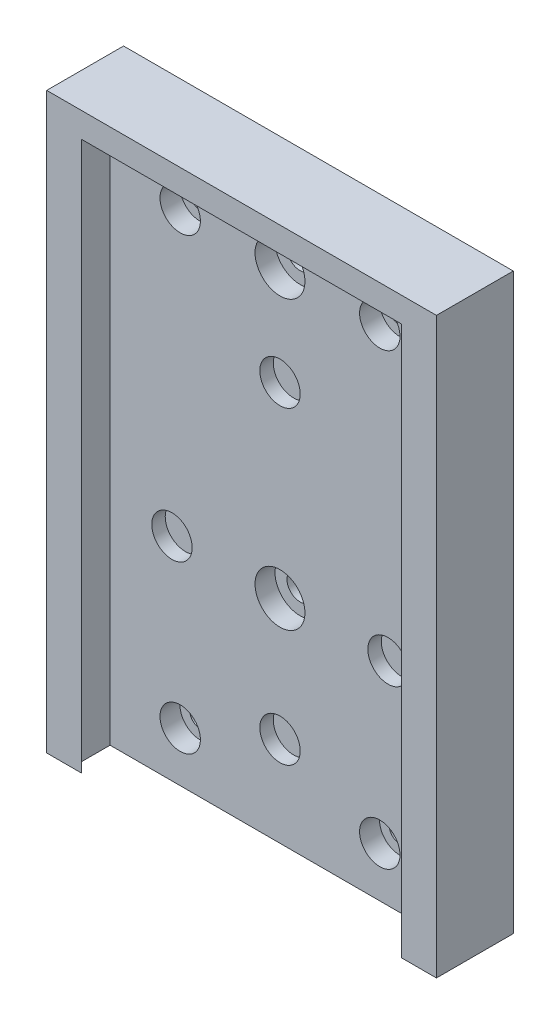
SolidWorks part; units mm, degrees
ref_plane "Front Plane" through (0, 0, 0) normal (0, 0, 1) x (1, 0, 0)
ref_plane "Top Plane" through (0, 0, 0) normal (0, 1, 0) x (1, 0, 0)
ref_plane "Right Plane" through (0, 0, 0) normal (1, 0, 0) x (0, 0, -1)
sketch "Sketch1" plane through (0, 0, 0) normal (0, 0, 1) x (1, 0, 0)
  line L0 (0, -45) -> (0, -41) construction
  line L5 (-34, 55) -> (34, -55) construction
  line L6 (-34, -55) -> (34, 55) construction
  line L7 (-20, 45) -> (20, 45) construction
  line L8 (-20, 45) -> (-20, -45) construction
  line L9 (-20, -45) -> (20, -45) construction
  line L10 (20, 45) -> (20, -45) construction
  line L11 (-20, 45) -> (20, -45) construction
  line L12 (-20, -45) -> (20, 45) construction
  line L13 (0, 25) -> (-21.6506, -12.5) construction
  line L14 (-21.6506, -12.5) -> (21.6506, -12.5) construction
  line L15 (21.6506, -12.5) -> (0, 25) construction
  line L16 (0, 45) -> (0, 55) construction
  line L17 (34.05, 55) -> (-34.05, 55)
  line L18 (0, 0) -> (-10.595, 0) construction
  line L19 (34.05, -55) -> (-34.05, -55)
  line L20 (34.05, -55) -> (34.05, 55)
  line L21 (-34.05, -55) -> (-34.05, 55)
  circle A0 centre (20, 45) radius 2.1
  circle A1 centre (-20, 45) radius 2.1
  circle A2 centre (20, -45) radius 2.1
  circle A3 centre (-20, -45) radius 2.1
  circle A4 centre (0, 0) radius 25 construction
  circle A5 centre (21.6506, -12.5) radius 4.05
  circle A6 centre (0, 25) radius 4.05
  circle A7 centre (-21.6506, -12.5) radius 4.05
  circle A9 centre (0, -36.95) radius 4.05
  circle A10 centre (0, 45) radius 2.6
  circle A11 centre (0, -12.5) radius 2.6
  point P0 (0, 0)
  point P6 (0, 0)
  point P35 (0, 55)
extrude "Boss-Extrude1" add sketch "Sketch1" along normal blind 7.7
sketch "Sketch2" plane through (0, 0, 0) normal (0, 0, -1) x (-1, 0, 0)
  circle A0 centre (-21.6506, -12.5) radius 6.3046
  circle A1 centre (0, 25) radius 7.3343
  circle A2 centre (21.6506, -12.5) radius 8.114
  circle A3 centre (0, -36.95) radius 11.0737
extrude "Boss-Extrude2" add sketch "Sketch2" against normal blind 5
sketch "Sketch3" plane through (0, 0, 7.7) normal (0, 0, -1) x (-1, 0, 0)
  circle A0 centre (-20, 45) radius 4.05
  circle A1 centre (20, 45) radius 4.05
  circle A2 centre (-20, -45) radius 4.05
  circle A3 centre (20, -45) radius 4.05
  circle A4 centre (0, 45) radius 5
  circle A5 centre (0, -12.5) radius 5
extrude "Cut-Extrude1" cut sketch "Sketch3" along normal blind 4
sketch "Sketch4" plane through (0, 0, 7.7) normal (0, 0, 1) x (1, 0, 0)
  line L5 (-34.05, 55) -> (34.05, 55)
  line L6 (-34.05, 55) -> (-34.05, 60)
  line L7 (-34.05, 60) -> (34.05, 60)
  line L8 (34.05, 55) -> (34.05, 60)
extrude "Boss-Extrude3" add sketch "Sketch4" along normal blind 7.7 and the other way blind 7.7
sketch "Sketch7" plane through (0, -55, 0) normal (0, -1, 0) x (1, 0, 0)
  line L0 (-34.05, 15.4) -> (-32.05, 15.4)
  line L1 (-34.05, 15.4) -> (34.05, 15.4) construction
  line L4 (-34.05, 15.4) -> (-39.05, 15.4)
  line L5 (-39.05, 15.4) -> (-39.05, 0)
  line L6 (-39.05, 0) -> (-34.05, 0)
  line L8 (0, 0) -> (0, 13.1137) construction
  line L9 (-34.05, 0) -> (34.05, 0) construction
  line L11 (39.05, 0) -> (34.05, 0)
  line L12 (39.05, 15.4) -> (39.05, 0)
  line L13 (34.05, 15.4) -> (39.05, 15.4)
  line L15 (34.05, 15.4) -> (32.05, 15.4)
  line L16 (-32.05, 15.4) -> (-34.05, 13.4)
  line L17 (-34.05, 7.7) -> (-34.05, 15.4) construction
  line L18 (-34.05, 13.4) -> (-34.05, 0)
  line L19 (34.05, 13.4) -> (34.05, 0)
  line L20 (32.05, 15.4) -> (34.05, 13.4)
extrude "Boss-Extrude4" add sketch "Sketch7" against normal up to surface (115 mm away) up to face at (0, 60, 7.7)
